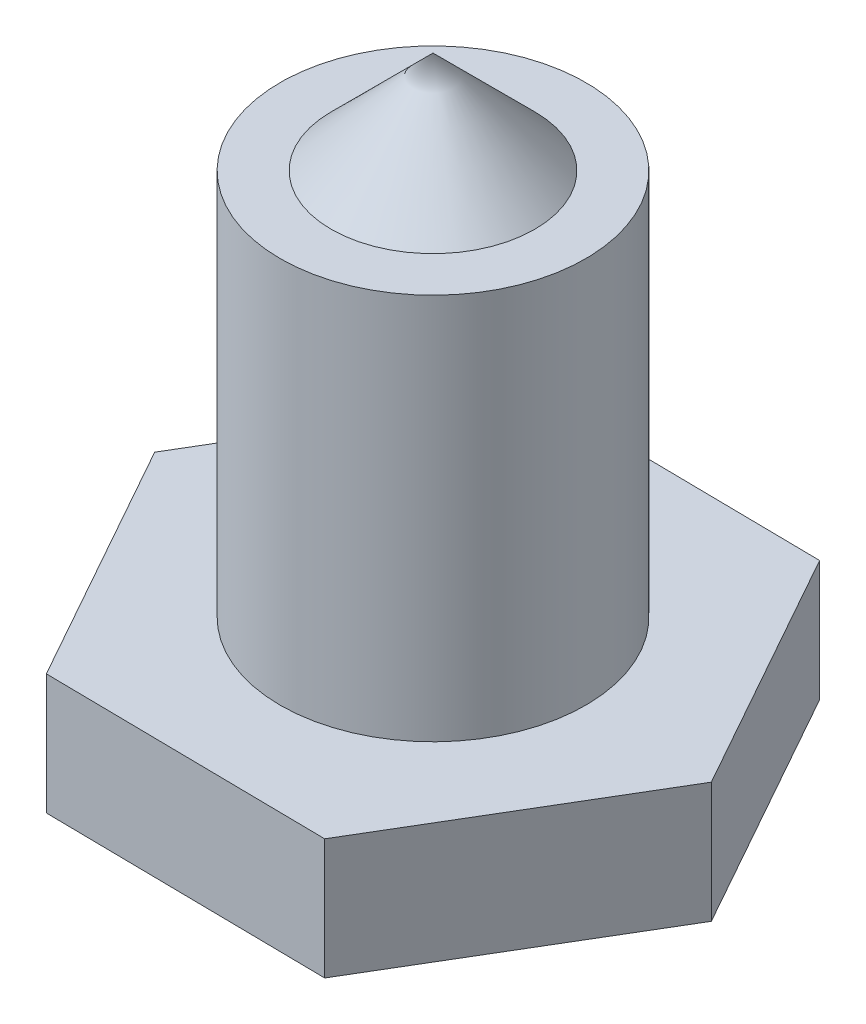
SolidWorks part; units mm, degrees
material "ABS"
ref_plane "Front Plane" through (0, 0, 0) normal (0, 0, 1) x (1, 0, 0)
ref_plane "Top Plane" through (0, 0, 0) normal (0, 1, 0) x (1, 0, 0)
ref_plane "Right Plane" through (0, 0, 0) normal (1, 0, 0) x (0, 0, -1)
sketch "Sketch1" plane through (0, 0, 0) normal (0, 1, 0) x (1, 0, 0)
  line L1 (5.6245, 9.4516) -> (-5.3731, 9.5967)
  line L2 (-5.3731, 9.5967) -> (-10.9976, 0.1451)
  line L3 (-10.9976, 0.1451) -> (-5.6245, -9.4516)
  line L4 (-5.6245, -9.4516) -> (5.3731, -9.5967)
  line L5 (5.3731, -9.5967) -> (10.9976, -0.1451)
  line L6 (10.9976, -0.1451) -> (5.6245, 9.4516)
  circle A0 centre (0, 0) radius 9.525 construction
  dimension "D1" = 19.05
extrude "Boss-Extrude1" add sketch "Sketch1" along normal blind 4.7
sketch "Sketch2" plane through (0, 4.7, 0) normal (0, 1, 0) x (1, 0, 0)
  circle A0 centre (0, 0) radius 5.9531
  dimension "D1" = 11.9062
extrude "Boss-Extrude2" add sketch "Sketch2" along normal blind 15.0812
sketch "Sketch3" plane through (0, 19.7812, 0) normal (0, 1, 0) x (1, 0, 0)
  circle A0 centre (0, 0) radius 6
  dimension "D1" = 12
sketch "Sketch4" plane through (0, 0, 0) normal (1, 0, 0) x (0, 0, -1)
  line L0 (0, 19.7812) -> (0, 23.75)
  line L1 (5.9531, 19.7812) -> (-5.9531, 19.7812) construction
  line L2 (0, 23.75) -> (3.9688, 19.7812)
  line L3 (3.9688, 19.7812) -> (0, 19.7812)
  dimension "D1" = 3.9688
  dimension "D2" = 3.9688
revolve "Revolve1" add sketch "Sketch4" angle 360 about L0
